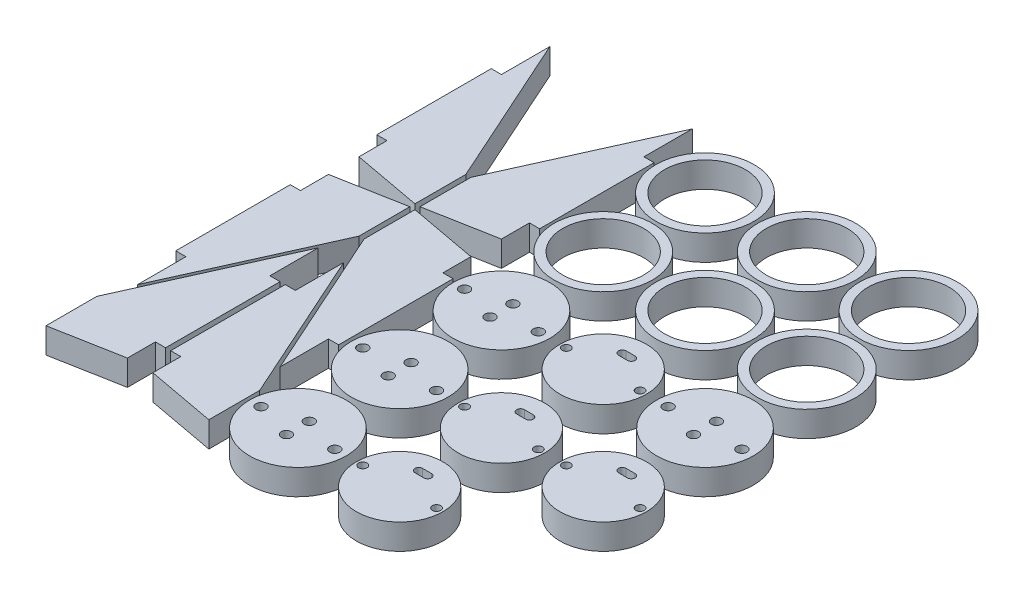
SolidWorks part; units mm, degrees
ref_plane "Front Plane" through (0, 0, 0) normal (0, 0, 1) x (1, 0, 0)
ref_plane "Top Plane" through (0, 0, 0) normal (0, 1, 0) x (1, 0, 0)
ref_plane "Right Plane" through (0, 0, 0) normal (1, 0, 0) x (0, 0, -1)
sketch "Sketch1" plane through (0, 0, 0) normal (0, 1, 0) x (1, 0, 0)
  line L1 (-225, -150) -> (225, -150)
  line L2 (-225, -150) -> (-225, 150)
  line L3 (-225, 150) -> (225, 150)
  line L4 (225, -150) -> (225, 150)
  line L5 (-225, -150) -> (225, 150) construction
  line L6 (-225, 150) -> (225, -150) construction
  point P0 (0, 0)
  dimension "D1" = 450
  dimension "D2" = 300
extrude "Boss-Extrude1" add sketch "Sketch1" along normal blind 10
sketch "Sketch3" plane through (0, 10, 0) normal (0, 1, 0) x (1, 0, 0)
  line L0 (-135.695, 125.695) -> (-95.695, 125.695) construction
  line L1 (-135.695, 125.695) -> (-135.695, 85.695) construction
  line L2 (-97.445, 54.945) -> (-93.945, 54.945) construction
  line L3 (-97.445, 56.445) -> (-93.945, 56.445)
  line L4 (-220, 126) -> (-216, 126)
  line L5 (-216, 126) -> (-216, 145)
  line L6 (-216, 145) -> (-189, 85)
  line L7 (-189, 85) -> (-189, 65)
  line L8 (220, -145) -> (220, 145)
  line L9 (220, 145) -> (-220, 145)
  line L10 (-220, 145) -> (-220, -145)
  line L11 (-220, -145) -> (220, -145)
  line L12 (220, -145) -> (220, 145)
  line L13 (220, 145) -> (0, 145)
  line L14 (-220, 126) -> (-220, 81)
  line L15 (0, -145) -> (220, -145)
  line L16 (-189, 65) -> (-216, 70)
  line L17 (-216, 70) -> (-216, 81)
  line L18 (-216, 81) -> (-220, 81)
  line L19 (-188, 65) -> (-188, 145) construction
  line L20 (-187, 65) -> (-160, 70)
  line L21 (-160, 81) -> (-156, 81)
  line L22 (-160, 70) -> (-160, 81)
  line L23 (-156, 126) -> (-160, 126)
  line L24 (-160, 126) -> (-160, 145)
  line L25 (-160, 145) -> (-187, 85)
  line L26 (-187, 85) -> (-187, 65)
  line L27 (-156, 126) -> (-156, 81)
  line L28 (-216, 58) -> (-216, 47)
  line L29 (-143.0318, 64) -> (-188.429, 64) construction
  line L30 (-216, 47) -> (-220, 47)
  line L31 (-220, 2) -> (-216, 2)
  line L32 (-216, 2) -> (-216, -17)
  line L33 (-216, -17) -> (-189, 43)
  line L34 (-189, 63) -> (-216, 58)
  line L35 (-189, 43) -> (-189, 63)
  line L36 (-187, 43) -> (-187, 63)
  line L37 (-160, -17) -> (-187, 43)
  line L38 (-160, 2) -> (-160, -17)
  line L39 (-156, 2) -> (-160, 2)
  line L40 (-156, 2) -> (-156, 47)
  line L41 (-160, 47) -> (-156, 47)
  line L42 (-160, 58) -> (-160, 47)
  line L43 (-187, 63) -> (-160, 58)
  line L44 (-97.445, 53.445) -> (-93.945, 53.445)
  line L45 (-97.445, 14.945) -> (-93.945, 14.945) construction
  line L46 (-97.445, 16.445) -> (-93.945, 16.445)
  line L47 (-97.445, 13.445) -> (-93.945, 13.445)
  line L48 (-135.695, 45.695) -> (-135.695, 5.695) construction
  line L49 (0, -145) -> (0, 145)
  line L50 (-220, -49) -> (-193, -44)
  line L51 (-193, -33) -> (-189, -33)
  line L52 (-193, -44) -> (-193, -33)
  line L53 (-189, 12) -> (-193, 12)
  line L54 (-193, 12) -> (-193, 31)
  line L55 (-193, 31) -> (-220, -29)
  line L57 (-189, 12) -> (-189, -33)
  line L58 (-183, -33) -> (-187, -33)
  line L59 (-183, -44) -> (-183, -33)
  line L60 (-156, -49) -> (-183, -44)
  line L61 (-183, 31) -> (-156, -29)
  line L62 (-183, 12) -> (-183, 31)
  line L63 (-187, 12) -> (-183, 12)
  line L64 (-187, 12) -> (-187, -33)
  line L65 (-156, -29) -> (-156, -49)
  line L66 (-97.445, -25.055) -> (-93.945, -25.055) construction
  line L67 (-97.445, -23.555) -> (-93.945, -23.555)
  line L68 (-97.445, -26.555) -> (-93.945, -26.555)
  line L69 (-220, 47) -> (-220, 2)
  line L70 (-220, -29) -> (-220, -49)
  line L71 (-57.445, 14.945) -> (-53.945, 14.945) construction
  line L72 (-57.445, 16.445) -> (-53.945, 16.445)
  line L73 (-57.445, 13.445) -> (-53.945, 13.445)
  circle A0 centre (-135.695, 125.695) radius 19.305
  circle A1 centre (-135.695, 125.695) radius 15.9
  circle A2 centre (-95.695, 125.695) radius 15.9
  circle A3 centre (-95.695, 125.695) radius 19.305
  circle A4 centre (-95.695, 85.695) radius 15.9
  circle A5 centre (-95.695, 85.695) radius 19.305
  circle A6 centre (-135.695, 85.695) radius 15.9
  circle A7 centre (-135.695, 85.695) radius 19.305
  circle A8 centre (-135.695, 45.695) radius 19
  circle A9 centre (-121.195, 45.695) radius 2
  circle A10 centre (-150.195, 45.695) radius 2
  circle A11 centre (-135.695, 50.195) radius 2
  circle A12 centre (-135.695, 41.195) radius 2
  circle A13 centre (-95.695, 45.695) radius 17
  circle A14 centre (-81.195, 45.695) radius 1.65
  circle A15 centre (-110.195, 45.695) radius 1.65
  arc A16 (-97.445, 56.445) -> (-97.445, 53.445) centre (-97.445, 54.945) ccw
  arc A17 (-93.945, 53.445) -> (-93.945, 56.445) centre (-93.945, 54.945) ccw
  circle A18 centre (-55.695, 125.695) radius 15.9
  circle A19 centre (-55.695, 125.695) radius 19.305
  circle A20 centre (-55.695, 85.695) radius 15.9
  circle A21 centre (-55.695, 85.695) radius 19.305
  circle A22 centre (-135.695, 5.695) radius 19
  circle A23 centre (-135.695, 1.195) radius 2
  circle A24 centre (-150.195, 5.695) radius 2
  circle A25 centre (-121.195, 5.695) radius 2
  circle A26 centre (-135.695, 10.195) radius 2
  circle A27 centre (-95.695, 5.695) radius 17
  circle A28 centre (-110.195, 5.695) radius 1.65
  circle A29 centre (-81.195, 5.695) radius 1.65
  arc A30 (-97.445, 16.445) -> (-97.445, 13.445) centre (-97.445, 14.945) ccw
  arc A31 (-93.945, 13.445) -> (-93.945, 16.445) centre (-93.945, 14.945) ccw
  circle A32 centre (-135.695, -34.305) radius 19
  circle A33 centre (-135.695, -38.805) radius 2
  circle A34 centre (-150.195, -34.305) radius 2
  circle A35 centre (-121.195, -34.305) radius 2
  circle A36 centre (-135.695, -29.805) radius 2
  circle A37 centre (-95.695, -34.305) radius 17
  circle A38 centre (-110.195, -34.305) radius 1.65
  circle A39 centre (-81.195, -34.305) radius 1.65
  arc A40 (-97.445, -23.555) -> (-97.445, -26.555) centre (-97.445, -25.055) ccw
  arc A41 (-93.945, -26.555) -> (-93.945, -23.555) centre (-93.945, -25.055) ccw
  circle A42 centre (-55.695, 50.195) radius 2
  circle A43 centre (-41.195, 45.695) radius 2
  circle A44 centre (-55.695, 41.195) radius 2
  circle A45 centre (-70.195, 45.695) radius 2
  circle A46 centre (-55.695, 45.695) radius 19
  circle A47 centre (-41.195, 5.695) radius 1.65
  circle A48 centre (-70.195, 5.695) radius 1.65
  circle A49 centre (-55.695, 5.695) radius 17
  arc A50 (-57.445, 16.445) -> (-57.445, 13.445) centre (-57.445, 14.945) ccw
  arc A51 (-53.945, 13.445) -> (-53.945, 16.445) centre (-53.945, 14.945) ccw
  point P69 (-95.695, 54.945)
  point P99 (-95.695, 14.945)
  point P113 (0, 0)
  point P142 (-95.695, -25.055)
  point P166 (-55.695, 14.945)
  line M58 (225, -150) -> (225, 150)
  line M59 (225, 150) -> (-225, 150)
  line M60 (-225, 150) -> (-225, -150)
  line M61 (-225, -150) -> (225, -150)
  dimension "D11" = 38.61
  dimension "D12" = 31.8
  dimension "D18" = 38
  dimension "D20" = 4
  dimension "D25" = 34
  dimension "D28" = 3.3
  dimension "D30" = 1.5
  dimension "D2" = 45
  dimension "D3" = 75
  dimension "D4" = 11
  dimension "D5" = 27
  dimension "D6" = 20
  dimension "D7" = 60
  dimension "D8" = 4
  dimension "D9" = 1
  dimension "D10" = 1
  dimension "D13" = 20.305
  dimension "D16" = 40
  dimension "D17" = 40
  dimension "D19" = 40
  dimension "D21" = 29
  dimension "D22" = 14.5
  dimension "D23" = 9
  dimension "D24" = 4.5
  dimension "D26" = 29
  dimension "D27" = 14.5
  dimension "D29" = 3.5
  dimension "D31" = 9.25
  dimension "D33" = 40
  dimension "D34" = 27
  dimension "D35" = 20
  dimension "D36" = 11
  dimension "D37" = 45
  dimension "D38" = 75
  dimension "D39" = 60
  dimension "D40" = 12
  dimension "D41" = 4
  dimension "D1" = 5
  dimension "D14" = 3
  dimension "D15" = 2
  dimension "D32" = 3
  dimension "D42" = 2
  dimension "D43" = 2
extrude "Cut-Extrude1" cut sketch "Sketch3" against normal blind 10 contours L49 L15 L12 L13 | A49 A46 A37 A32 A27 A22 A21 A19 A13 A8 A7 A5 A3 A0 L70 L55 L54 L53 L57 L51 L52 L50 L69 L30 L28 L34 L35 L33 L32 L31 M61 M58 M59 M60 | A1 | A2 | A18 | A20 | A4 | A6 | A11 | A12 | A9 | A10 | A15 | L44 A17 L3 A16 | A14 | A43 | A42 | A44 | A45 | A47 | L73 A51 L72 A50 | A48 | A29 | L47 A31 L46 A30 | A28 | A25 | A26 | A24 | A23 | A34 | A36 | A33 | A35 | A38 | L68 A41 L67 A40 | A39
